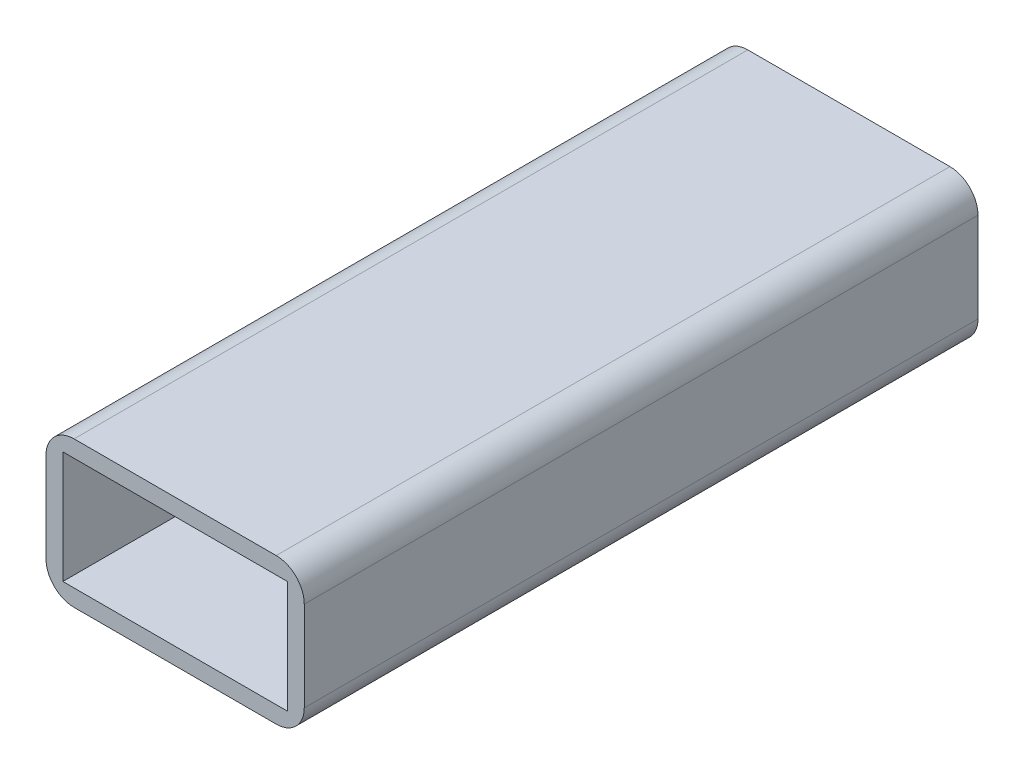
SolidWorks part; units mm, degrees
ref_plane "Front Plane" through (0, 0, 0) normal (0, 0, 1) x (1, 0, 0)
ref_plane "Top Plane" through (0, 0, 0) normal (0, 1, 0) x (1, 0, 0)
ref_plane "Right Plane" through (0, 0, 0) normal (1, 0, 0) x (0, 0, -1)
sketch "Sketch1" plane through (0, 0, 0) normal (0, 0, 1) x (1, 0, 0)
  line L1 (20, -10) -> (-20, -10)
  line L2 (20, -10) -> (20, 10)
  line L3 (20, 10) -> (-20, 10)
  line L4 (-20, -10) -> (-20, 10)
  line L5 (20, -10) -> (-20, 10) construction
  line L6 (20, 10) -> (-20, -10) construction
  point P0 (0, 0)
  dimension "D1" = 40
  dimension "D2" = 20
extrude "Extrude-Thin1" add sketch "Sketch1" along normal blind 120 thin thin type one direction wall 3
fillet "Fillet2" radius 5 4 edges at (23, -13, 60) (23, 13, 60) (-23, 13, 60) (-23, -13, 60)
sketch "Sketch3" plane through (0, 13, 0) normal (0, 1, 0) x (1, 0, 0)
  line L0 (0, -17.323) -> (0, -107.323) construction
  line L1 (6, -17.323) -> (6, -107.323)
  line L2 (-6, -17.323) -> (-6, -107.323)
  arc A0 (6, -17.323) -> (-6, -17.323) centre (0, -17.323) ccw
  arc A1 (-6, -107.323) -> (6, -107.323) centre (0, -107.323) ccw
  point P3 (0, -62.323)
  dimension "D2" = 6
  dimension "D1" = 90
extrude "Cut-Extrude1" [suppressed] cut sketch "Sketch3" against normal blind 4
